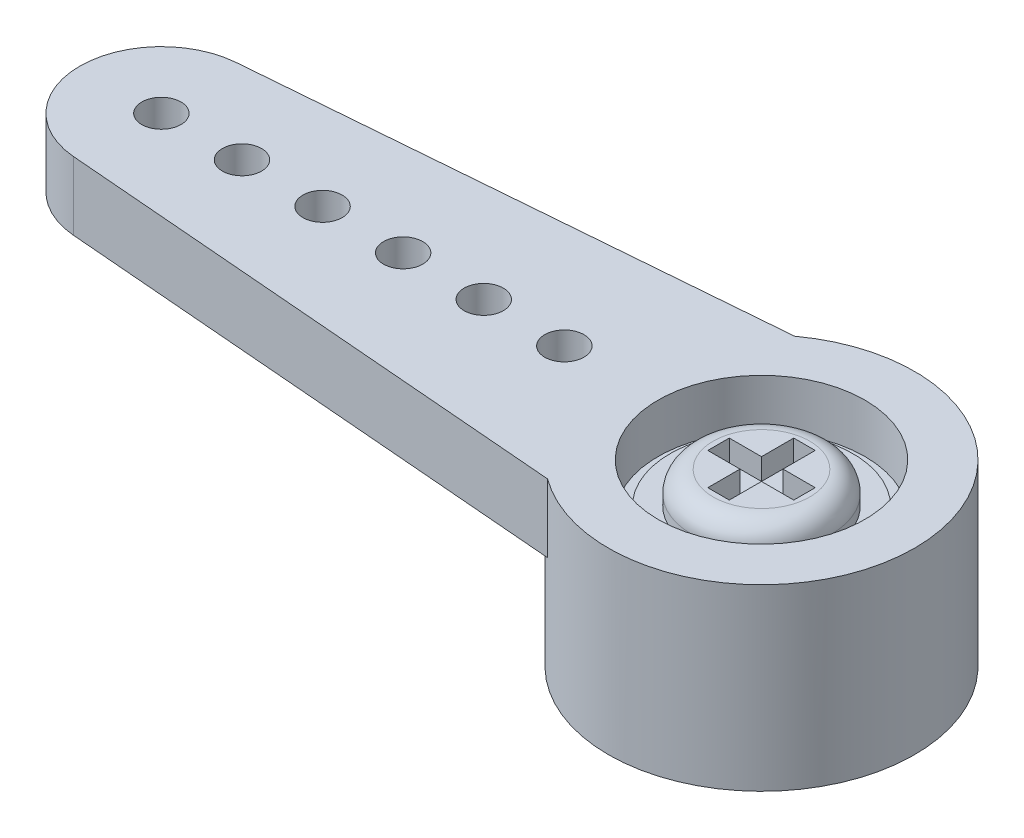
SolidWorks part; units mm, degrees
material "Nylon 101"
ref_plane "Front Plane" through (0, 0, 0) normal (0, 0, 1) x (1, 0, 0)
ref_plane "Top Plane" through (0, 0, 0) normal (0, 1, 0) x (1, 0, 0)
ref_plane "Right Plane" through (0, 0, 0) normal (1, 0, 0) x (0, 0, -1)
sketch "Sketch18" plane through (0, 0, 0) normal (0, 1, 0) x (1, 0, 0)
  line L0 (-16.1163, 0) -> (3.6195, 0) construction
  line L1 (-14.3431, 1.924) -> (-2.1374, 2.921)
  line L2 (-14.3431, -1.924) -> (-2.1374, -2.921)
  arc A0 (-2.1374, -2.921) -> (-2.1374, 2.921) centre (0, 0) ccw
  arc A1 (-14.3431, 1.924) -> (-14.3431, -1.924) centre (-14.1859, 0) ccw
  dimension "D1" = 1.9304
  dimension "D2" = 3.6195
  dimension "D3" = 19.7358
  dimension "D4" = 5.842
extrude "Extrude17" add sketch "Sketch18" along normal blind 1.6129
sketch "Sketch19" plane through (0, 1.6129, 0) normal (0, 1, 0) x (1, 0, 0)
  circle A0 centre (0, 0) radius 3.6195
  arc A1 (-2.1374, -2.921) -> (-2.1374, 2.921) centre (0, 0) ccw construction
extrude "Extrude19" add sketch "Sketch19" against normal blind 4.2291
sketch "Sketch20" plane through (0, 1.6129, 0) normal (0, 1, 0) x (1, 0, 0)
  line L0 (-14.1859, 0) -> (-12.2809, 0) construction
  line L1 (-12.2809, 0) -> (-10.3759, 0) construction
  line L2 (-10.3759, 0) -> (-8.4709, 0) construction
  line L3 (-8.4709, 0) -> (-6.5659, 0) construction
  line L4 (-6.5659, 0) -> (-4.6609, 0) construction
  line L5 (-4.6609, 0) -> (-2.7559, 0) construction
  line L6 (-2.7559, 0) -> (0, 0) construction
  circle A0 centre (-14.1859, 0) radius 0.4636
  circle A1 centre (0, 0) radius 1.27
  circle A3 centre (-4.6609, 0) radius 0.4636
  circle A4 centre (-6.5659, 0) radius 0.4636
  circle A5 centre (-8.4709, 0) radius 0.4636
  circle A6 centre (-10.3759, 0) radius 0.4636
  circle A7 centre (-12.2809, 0) radius 0.4636
  dimension "D1" = 0.9271
  dimension "D3" = 2.54
  dimension "D2" = 1.905
extrude "Extrude20" cut sketch "Sketch20" against normal through all
sketch "Sketch21" plane through (0, 1.6129, 0) normal (0, 1, 0) x (1, 0, 0)
  circle A0 centre (0, 0) radius 2.4447
  dimension "D1" = 4.8895
extrude "Extrude21" cut sketch "Sketch21" against normal blind 1.1557
sketch "Sketch22" plane through (0, -2.6162, 0) normal (0, -1, 0) x (1, 0, 0)
  circle A0 centre (0, 0) radius 2.286
  dimension "D1" = 4.572
extrude "Extrude22" cut sketch "Sketch22" against normal blind 2.3368
sketch "Sketch23" plane through (0, 0.4572, 0) normal (0, 1, 0) x (1, 0, 0)
  circle A0 centre (0, 0) radius 2.159
  dimension "D1" = 4.318
extrude "Extrude23" add sketch "Sketch23" along normal blind 0.2032 separate body
sketch "Sketch24" plane through (0, 0.6604, 0) normal (0, 1, 0) x (1, 0, 0)
  circle A0 centre (0, 0) radius 1.651
  dimension "D1" = 3.302
extrude "Extrude24" add sketch "Sketch24" along normal blind 0.762
sketch "Sketch25" plane through (0, 1.4224, 0) normal (0, 1, 0) x (1, 0, 0)
  line L0 (0, -1.651) -> (0, 1.651) construction
  line L1 (-1.651, 0) -> (1.651, 0) construction
  line L2 (0.254, -1.016) -> (-0.254, -1.016)
  line L3 (-0.254, -1.016) -> (-0.254, -0.254)
  line L4 (-0.254, -0.254) -> (-1.016, -0.254)
  line L5 (-1.016, -0.254) -> (-1.016, 0.254)
  line L6 (0.254, 1.016) -> (-0.254, 1.016)
  line L7 (-0.254, 1.016) -> (-0.254, 0.254)
  line L8 (-0.254, 0.254) -> (-1.016, 0.254)
  line L9 (0.254, 1.016) -> (0.254, 0.254)
  line L10 (0.254, -1.016) -> (0.254, -0.254)
  line L11 (0.254, -0.254) -> (1.016, -0.254)
  line L12 (1.016, -0.254) -> (1.016, 0.254)
  line L13 (0.254, 0.254) -> (1.016, 0.254)
  circle A0 centre (0, 0) radius 1.651 construction
  point P16 (-1.016, 0)
  point P17 (0, 1.016)
  point P19 (0, -1.016)
  dimension "D1" = 2.032
  dimension "D2" = 0.508
extrude "Extrude25" cut sketch "Sketch25" against normal blind 0.508
fillet "Fillet1" radius 0.508 1 edges at (0, 1.4224, 1.651)
sketch "Sketch26" plane through (0, 1.6129, 0) normal (0, 1, 0) x (1, 0, 0)
  line L6 (-14.1859, -0.0068) -> (-12.2809, -0.0059) construction
  line L7 (-12.2809, -0.0059) -> (-10.3759, -0.005) construction
  line L8 (-10.3759, -0.005) -> (-8.4709, -0.0041) construction
  line L9 (-8.4709, -0.0041) -> (-6.5659, -0.0031) construction
  line L10 (-6.5659, -0.0031) -> (-4.6609, -0.0022) construction
  line L11 (-4.6609, -0.0022) -> (0, 0) construction
  circle A3 centre (-4.6609, -0.0022) radius 2.05
  circle A4 centre (-12.2809, -0.0059) radius 2.05
  point P0 (-14.1859, -0.0059)
  dimension "D5" = 4.1
  dimension "D6" = 4.1
  dimension "D7" = 1.905
  dimension "D8" = 4.6609
